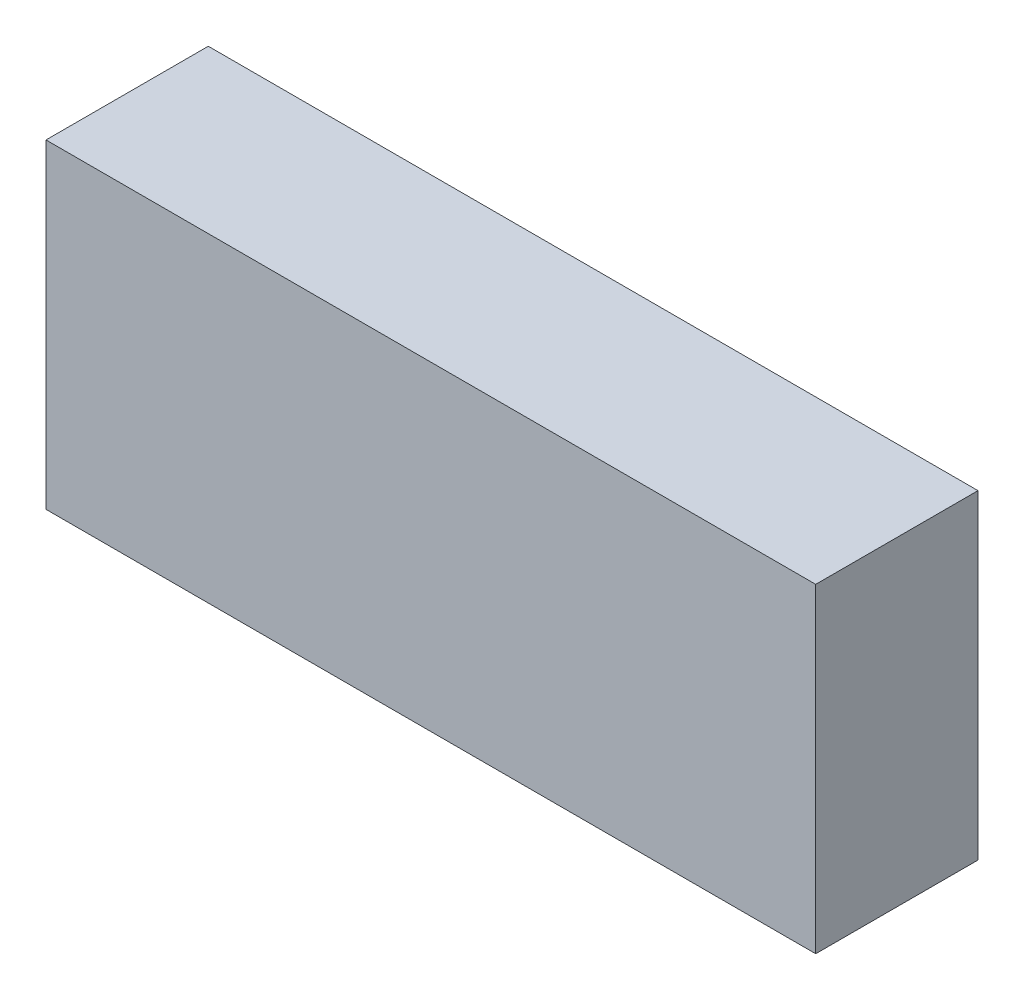
SolidWorks part; units mm, degrees
ref_plane "Front Plane" through (0, 0, 0) normal (0, 0, 1) x (1, 0, 0)
ref_plane "Top Plane" through (0, 0, 0) normal (0, 1, 0) x (1, 0, 0)
ref_plane "Right Plane" through (0, 0, 0) normal (1, 0, 0) x (0, 0, -1)
sketch "Sketch1" plane through (0, 0, 0) normal (0, 1, 0) x (1, 0, 0)
  line L1 (0, 0) -> (166, 0)
  line L2 (0, 0) -> (0, 35)
  line L3 (0, 35) -> (166, 35)
  line L4 (166, 0) -> (166, 35)
  dimension "D1" = 166
  dimension "D2" = 35
extrude "Boss-Extrude1" add sketch "Sketch1" along normal blind 69
